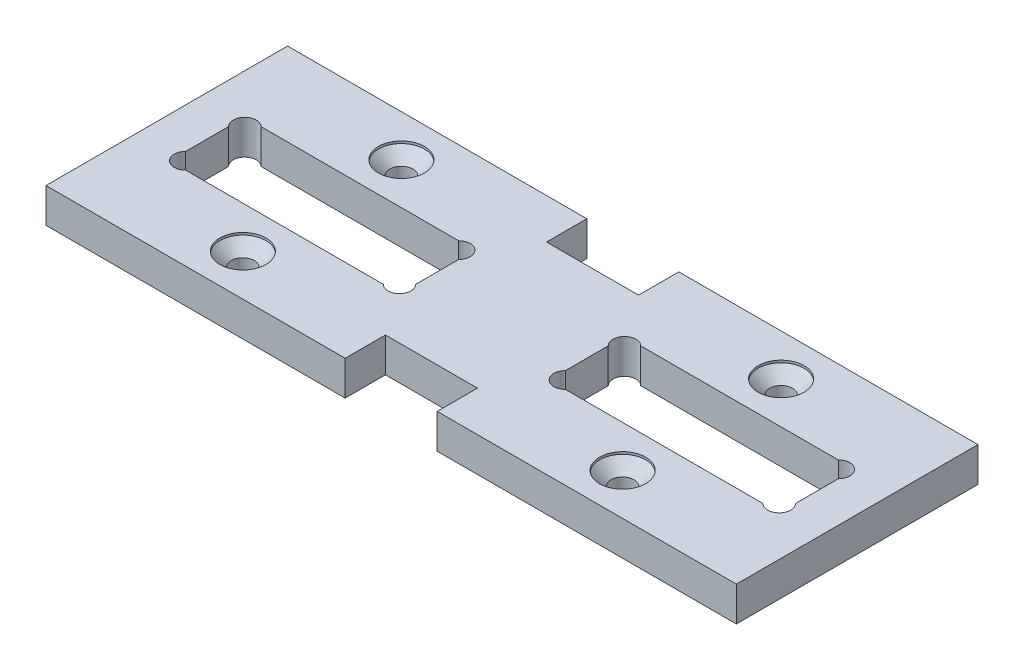
SolidWorks part; units mm, degrees
ref_plane "Front Plane" through (0, 0, 0) normal (0, 0, 1) x (1, 0, 0)
ref_plane "Top Plane" through (0, 0, 0) normal (0, 1, 0) x (1, 0, 0)
ref_plane "Right Plane" through (0, 0, 0) normal (1, 0, 0) x (0, 0, -1)
sketch "Sketch1" plane through (0, 0, 0) normal (0, 1, 0) x (1, 0, 0)
  line L0 (-30, 7) -> (30, 7)
  line L1 (-30, 10.5) -> (30, 10.5)
  line L2 (-30, 10.5) -> (-30, -10.5)
  line L3 (-30, -10.5) -> (30, -10.5)
  line L4 (30, 10.5) -> (30, -10.5)
  line L5 (-30, 10.5) -> (30, -10.5) construction
  line L6 (-30, -10.5) -> (30, 10.5) construction
  line L7 (-4, -10.5) -> (4, -10.5)
  line L8 (-4, -10.5) -> (-4, 10.5)
  line L9 (-4, 10.5) -> (4, 10.5)
  line L10 (4, -10.5) -> (4, 10.5)
  line L11 (-4, -10.5) -> (4, 10.5) construction
  line L12 (-4, 10.5) -> (4, -10.5) construction
  line L13 (-30, 0) -> (30, 0) construction
  line L14 (-30, -7) -> (30, -7)
  line L15 (-6.5, 3.275) -> (-13.05, -3.275) construction
  line L16 (-26.5, 3.275) -> (-6.5, 3.275)
  line L17 (-26.5, 3.275) -> (-26.5, -3.275)
  line L18 (-26.5, -3.275) -> (-6.5, -3.275)
  line L19 (-6.5, 3.275) -> (-6.5, -3.275)
  line L20 (-26.5, 3.275) -> (-6.5, -3.275) construction
  line L21 (-26.5, -3.275) -> (-6.5, 3.275) construction
  line L22 (-16.5, 3.275) -> (-16.5, -3.275) construction
  line L23 (0, 10.5) -> (0, -10.5) construction
  line L24 (26.5, 3.275) -> (26.5, -3.275)
  line L25 (26.5, 3.275) -> (6.5, 3.275)
  line L26 (6.5, 3.275) -> (6.5, -3.275)
  line L27 (26.5, -3.275) -> (6.5, -3.275)
  line L28 (-16.5, 3.275) -> (-16.5, 10.5) construction
  circle A0 centre (-7.2071, 2.5679) radius 1
  circle A1 centre (-7.2071, -2.5679) radius 1
  circle A2 centre (-25.7929, 2.5679) radius 1
  circle A3 centre (-25.7929, -2.5679) radius 1
  circle A4 centre (7.2071, -2.5679) radius 1
  circle A5 centre (7.2071, 2.5679) radius 1
  circle A6 centre (25.7929, 2.5679) radius 1
  circle A7 centre (25.7929, -2.5679) radius 1
  circle A8 centre (-16.5, 6.8875) radius 1
  circle A9 centre (-16.5, -6.8875) radius 1
  circle A10 centre (16.5, 6.8875) radius 1
  circle A11 centre (16.5, -6.8875) radius 1
  point P0 (0, 0)
  point P6 (0, 0)
  point P17 (-16.5, 0)
  dimension "D8" = 2
  dimension "D10" = 2
  dimension "D1" = 21
  dimension "D2" = 60
  dimension "D3" = 8
  dimension "D4" = 3.5
  dimension "D5" = 20
  dimension "D6" = 6.55
  dimension "D7" = 45
  dimension "D9" = 13
extrude "Boss-Extrude1" add sketch "Sketch1" along normal blind 3 contours L0 L8 L1 L2 | L2 L14 L8 L0 | L14 L2 L3 L8 | L8 L14 L10 L0 | L10 L14 L4 L0 | L10 L0 L4 L1 | L14 L10 L3 L4
hole_wizard "CSK for M2 Flat Head Machine Screw1" positions "Sketch2" profile "Sketch3" countersink size "M2" standard "ANSI Metric" end condition through all
sketch "Sketch2" plane through (0, 3, 0) normal (0, 1, 0) x (1, 0, 0)
  point P0 (-16.5, 6.8875)
  point P3 (-16.5, -6.8875)
  point P6 (16.5, 6.8875)
  point P9 (16.5, -6.8875)
sketch "Sketch3" plane through (-16.5, 3, -6.8875) normal (1, 0, 0) x (0, 0, 1)
  line L0 (0, 0) -> (0, 3)
  line L1 (0, 3) -> (1, 3)
  line L2 (1, 3) -> (1, 1.2)
  line L3 (1, 1.2) -> (2, 0.2)
  line L4 (2, 0.2) -> (2, 0)
  line L6 (2, 0) -> (0, 0)
  line L7 (-1, 1.2) -> (-2, 0.2) construction
  line L11 (0, -6.35) -> (0, 107.95) construction
  dimension "Thru Hole Dia." = 2
  dimension "Thru Hole Depth" = 3
  dimension "C'Sink Dia." = 4
  dimension "C'Sink Angle" = 90
  dimension "Head Clearance" = 0.2
